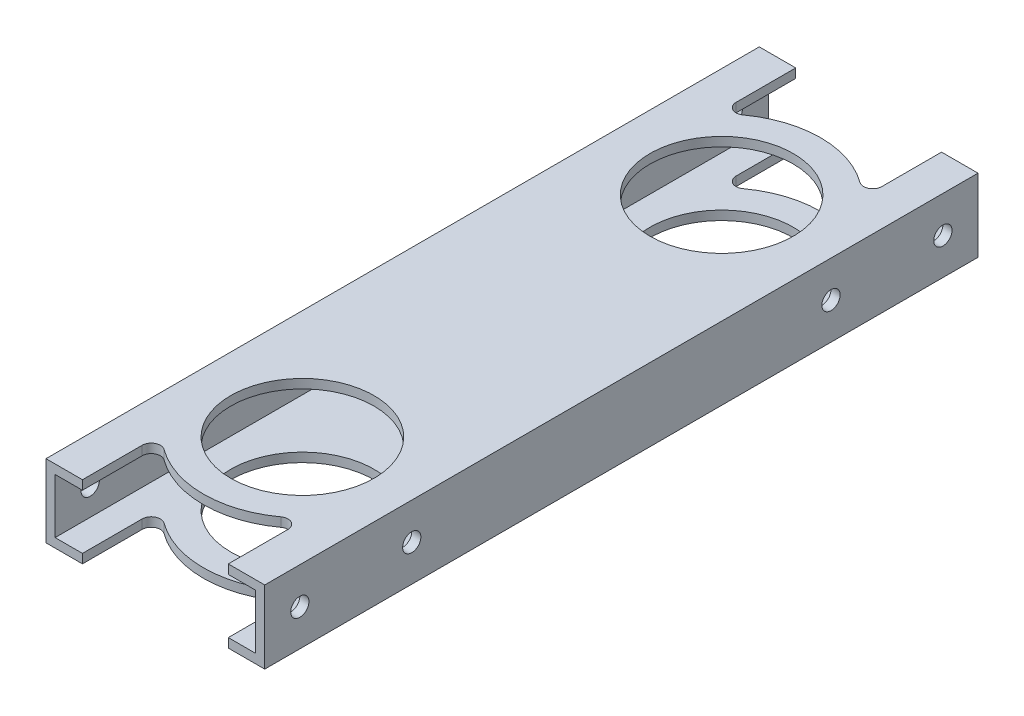
SolidWorks part; units mm, degrees
ref_plane "Front" through (0, 0, 0) normal (0, 0, 1) x (1, 0, 0)
ref_plane "Top" through (0, 0, 0) normal (0, 1, 0) x (1, 0, 0)
ref_plane "Right" through (0, 0, 0) normal (1, 0, 0) x (0, 0, -1)
sketch "Sketch1" plane through (0, 0, 0) normal (0, 0, 1) x (1, 0, 0)
  line L1 (-38.1, -12.7) -> (38.1, -12.7)
  line L2 (-38.1, -12.7) -> (-38.1, 12.7)
  line L3 (-38.1, 12.7) -> (38.1, 12.7)
  line L4 (38.1, -12.7) -> (38.1, 12.7)
  line L5 (-38.1, -12.7) -> (38.1, 12.7) construction
  line L6 (-38.1, 12.7) -> (38.1, -12.7) construction
  point P0 (0, 0)
  dimension "D1" = 25.4
  dimension "D2" = 76.2
extrude "Extrude-Thin1" add sketch "Sketch1" along normal blind 279.4 thin thin type one direction reverse wall 3.175
ref_plane "Plane3" through (0, 0, 0) normal (0, 0, -1) x (-1, 0, 0)
sketch "Sketch3" plane through (0, 12.7, 0) normal (0, 1, 0) x (1, 0, 0)
  line L0 (38.1, -279.4) -> (-38.1, -279.4) construction
  line L1 (38.1, -11.43) -> (27.4499, -11.43)
  line L2 (38.1, -279.4) -> (38.1, 0) construction
  line L3 (-27.4499, -11.43) -> (-38.1, -11.43)
  line L4 (-38.1, -279.4) -> (-38.1, 0) construction
  line L6 (38.1, -290.83) -> (27.4499, -290.83)
  line L7 (-27.4499, -290.83) -> (-38.1, -290.83)
  circle A0 centre (0, 0) radius 29.7345
  circle A1 centre (0, -279.4) radius 29.7345
  line M3 (38.1, 0) -> (-38.1, 0)
  line M5 (-38.1, -279.4) -> (38.1, -279.4)
  dimension "D1" = 59.469
  dimension "D2" = 11.43
  dimension "D3" = 11.43
extrude "Cut-Extrude2" cut sketch "Sketch3" against normal through all contours A1 M5 | A0 M3
sketch "Sketch4" plane through (0, 12.7, 0) normal (0, 1, 0) x (1, 0, 0)
  line L0 (0, -29.7345) -> (0, -249.6655) construction
  line L1 (-29.7345, -279.4) -> (29.7345, -279.4) construction
  circle A0 centre (0, -212.725) radius 24.972
  circle A1 centre (0, -66.675) radius 24.972
  arc A4 (29.7345, -279.4) -> (-29.7345, -279.4) centre (0, -279.4) ccw construction
  arc A5 (-29.7345, 0) -> (29.7345, 0) centre (0, 0) ccw construction
  point P16 (24.972, -66.675)
  point P17 (0, -279.4)
  dimension "D1" = 49.944
  dimension "D2" = 66.675
  dimension "D3" = 66.675
extrude "Cut-Extrude3" cut sketch "Sketch4" against normal through all
sketch "Sketch6" plane through (0, 12.7, 0) normal (0, 1, 0) x (1, 0, 0)
  line L1 (-38.1, -139.7) -> (38.1, -139.7) construction
  line L3 (-38.1, -279.4) -> (-38.1, 0) construction
  line L4 (-38.1, -15.459) -> (-25.4, -15.459)
  line L8 (-25.4, -15.459) -> (-25.4, -43.3323)
  line L10 (-38.1, -279.4) -> (-38.1, 0) construction
  line L12 (25.4, -43.3323) -> (25.4, -15.459)
  line L13 (-38.1, 0) -> (38.1, 0)
  line L14 (-38.1, 0) -> (-38.1, -15.459)
  line L15 (25.4, -15.459) -> (38.1, -15.459)
  line L18 (38.1, 0) -> (38.1, -15.459)
  line L19 (38.1, -279.4) -> (38.1, 0) construction
  arc A0 (25.4, -36.2574) -> (20.3519, -38.821) centre (22.225, -36.2574) cw
  arc A1 (-25.4, -36.2574) -> (-20.3519, -38.821) centre (-22.225, -36.2574) ccw
  circle A2 centre (0, -66.675) radius 34.497
  circle A4 centre (0, -66.675) radius 34.497
  arc A5 (-29.7345, 0) -> (29.7345, 0) centre (0, 0) ccw construction
  point P4 (-25.4, -15.459)
  point P23 (25.2813, -15.6524)
  dimension "D5" = 3.175
  dimension "D6" = 3.175
  dimension "D1" = 12.7
  dimension "D2" = 12.7
  dimension "D3" = 9.525
extrude "Cut-Extrude7" cut sketch "Sketch6" against normal through all
sketch "Sketch7" plane through (38.1, 0, 0) normal (1, 0, 0) x (0, 0, -1)
  line L0 (0, 0) -> (-27.686, 0) construction
  circle A0 centre (-27.686, 0) radius 3.175
  dimension "D1" = 6.35
  dimension "D2" = 27.686
extrude "Cut-Extrude8" cut sketch "Sketch7" against normal through all
ref_plane "Plane2" through (0, 0, 139.7) normal (0, 0, 1) x (1, 0, 0)
mirror "Mirror3" about plane through (0, 0, 139.7) normal (0, 0, 1) of "Cut-Extrude8", "Cut-Extrude7"
sketch "Sketch8" plane through (38.1, 0, 0) normal (1, 0, 0) x (0, 0, -1)
  line L0 (-15.459, 0) -> (-66.675, 0) construction
  line L1 (-15.459, -12.7) -> (-15.459, 12.7) construction
  line L2 (-139.7, -12.7) -> (-139.7, 12.7) construction
  line L3 (-263.941, -12.7) -> (-15.459, -12.7) construction
  line L4 (-263.941, 12.7) -> (-15.459, 12.7) construction
  line L5 (-41.703, 12.7) -> (-91.647, 12.7) construction
  line L6 (-41.703, 12.7) -> (-91.647, 12.7) construction
  line L7 (-66.675, 12.7) -> (-66.675, 0) construction
  circle A0 centre (-66.675, 0) radius 3.175
  circle A1 centre (-212.725, 0) radius 3.175
  dimension "D2" = 6.35
extrude "Cut-Extrude9" cut sketch "Sketch8" against normal through all
equation "\"D3@Sketch3\"=\"D2@Sketch3\""
equation "\"D2@Sketch6\"=\"D1@Sketch6\""
equation "\"D3@Sketch4\"=\"D2@Sketch4\""
